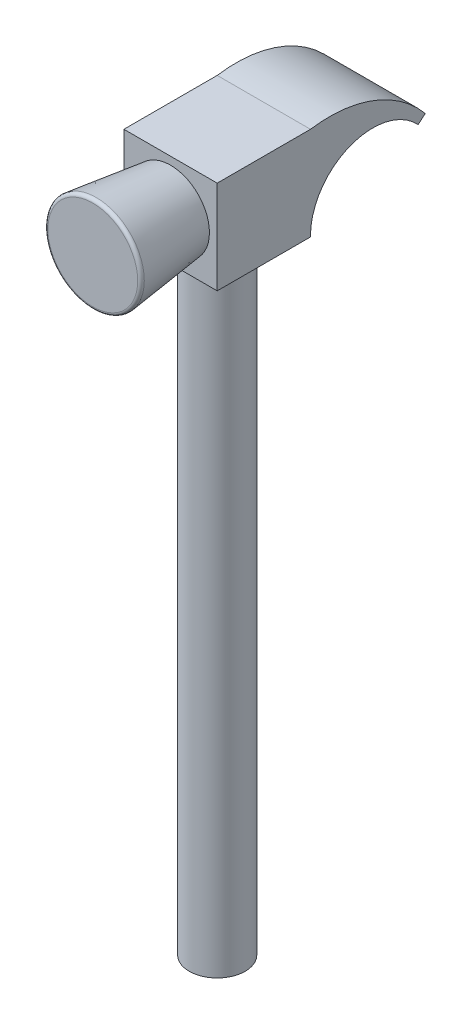
SolidWorks part; units mm, degrees
ref_plane "Front Plane" through (0, 0, 0) normal (0, 0, 1) x (1, 0, 0)
ref_plane "Top Plane" through (0, 0, 0) normal (0, 1, 0) x (1, 0, 0)
ref_plane "Right Plane" through (0, 0, 0) normal (1, 0, 0) x (0, 0, -1)
sketch "Sketch1" plane through (0, 0, 0) normal (0, 1, 0) x (1, 0, 0)
  circle A0 centre (0, 0) radius 9
  dimension "D1" = 18
extrude "Boss-Extrude1" add sketch "Sketch1" along normal blind 200
sketch "Sketch2" plane through (0, 200, 0) normal (0, 1, 0) x (1, 0, 0)
  line L1 (-15, -15) -> (15, -15)
  line L2 (-15, -15) -> (-15, 15)
  line L3 (-15, 15) -> (15, 15)
  line L4 (15, -15) -> (15, 15)
  line L5 (-15, -15) -> (15, 15) construction
  line L6 (-15, 15) -> (15, -15) construction
  point P0 (0, 0)
  dimension "D1" = 30
  dimension "D2" = 30
extrude "Boss-Extrude2" add sketch "Sketch2" along normal blind 30
sketch "Sketch6" plane through (0, 0, 15) normal (0, 0, 1) x (1, 0, 0)
  line L0 (0, 230) -> (0, 200) construction
  line L1 (-15, 230) -> (15, 230) construction
  line L2 (-15, 200) -> (15, 200) construction
  line L3 (-15, 215) -> (15, 215) construction
  line L4 (-15, 230) -> (-15, 200) construction
  line L5 (15, 230) -> (15, 200) construction
  circle A0 centre (0, 215) radius 12.5
  dimension "D1" = 25
extrude "Boss-Extrude3" add sketch "Sketch6" along normal blind 25 draft 7 draft outward yes
sketch "Sketch9" plane through (0, 0, 0) normal (0, 0, 1) x (1, 0, 0)
  line L0 (0, 228.7156) -> (0, 215)
sketch "Sketch11" plane through (0, 0, 0) normal (1, 0, 0) x (0, 0, -1)
  line L0 (51.9167, 215.9328) -> (49.6186, 214.0044)
  line L1 (15, 230) -> (15, 200) construction
  line L2 (15, 230) -> (-15, 230) construction
  line L7 (-15, 200) -> (15, 200)
  line L8 (-15, 230) -> (-15, 200)
  line L9 (15, 230) -> (-15, 230)
  line L10 (15, 200) -> (15, 230)
  line L14 (15, 200) -> (15, 230)
  arc A0 (15, 230) -> (51.9167, 215.9328) centre (21.0833, 190.4906) cw
  arc A1 (49.6186, 214.0044) -> (15, 200) centre (34.9968, 200.3588) ccw
  point P6 (0, 0)
  point P8 (15, 230)
  point P12 (21.1047, 190.4939)
  point P13 (0, 0)
  point P14 (21.0588, 190.4868)
  dimension "D2" = 20
  dimension "D1" = 3
  dimension "D3" = 40
  dimension "D4" = 0
extrude "Boss-Extrude4" add sketch "Sketch11" along normal blind 15 and the other way blind 15 contours A1 L0 A0 L14
fillet "Fillet1" radius 1 1 edges at (15.5696, 215, 40)
